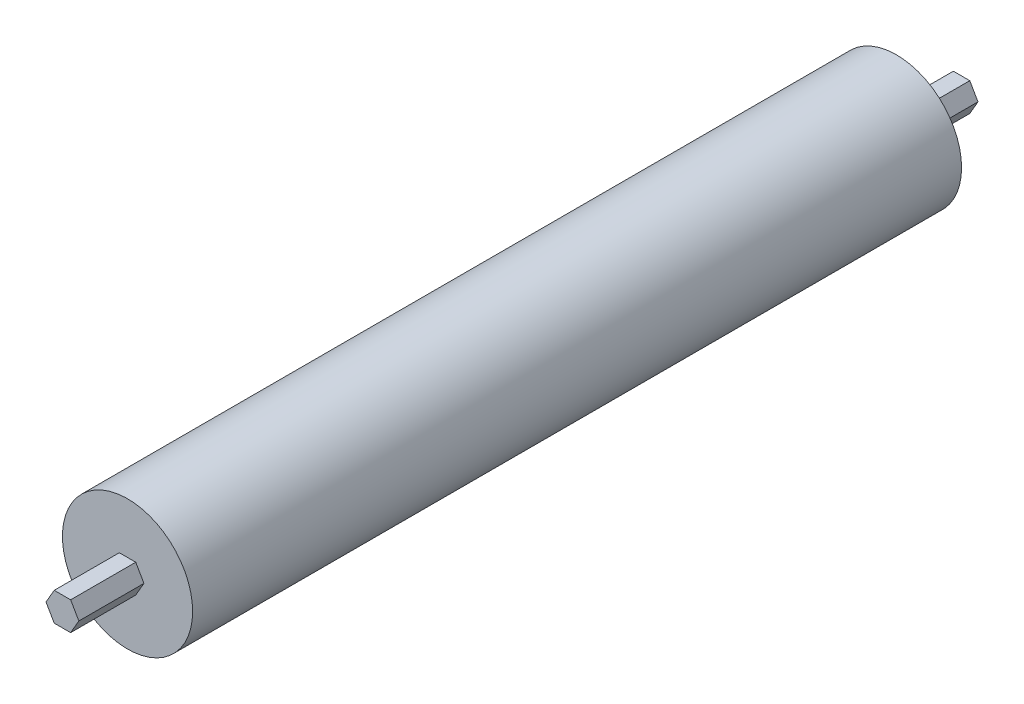
SolidWorks part; units mm, degrees
material "1060 Alloy"
ref_plane "Front Plane" through (0, 0, 0) normal (0, 0, 1) x (1, 0, 0)
ref_plane "Top Plane" through (0, 0, 0) normal (0, 1, 0) x (1, 0, 0)
ref_plane "Right Plane" through (0, 0, 0) normal (1, 0, 0) x (0, 0, -1)
sketch "Sketch1" plane through (0, 0, 0) normal (0, 0, 1) x (1, 0, 0)
  circle A0 centre (0, 0) radius 25.4
  dimension "D1" = 50.8
extrude "Boss-Extrude1" add sketch "Sketch1" along normal blind 300
sketch "Sketch2" plane through (0, 0, 300) normal (0, 0, 1) x (1, 0, 0)
  line L1 (6.4086, 0) -> (3.2043, 5.55)
  line L2 (3.2043, 5.55) -> (-3.2043, 5.55)
  line L3 (-3.2043, 5.55) -> (-6.4086, 0)
  line L4 (-6.4086, 0) -> (-3.2043, -5.55)
  line L5 (-3.2043, -5.55) -> (3.2043, -5.55)
  line L6 (3.2043, -5.55) -> (6.4086, 0)
  circle A0 centre (0, 0) radius 5.55 construction
  dimension "D1" = 11.1
extrude "Boss-Extrude2" add sketch "Sketch2" along normal blind 25.4
sketch "Sketch3" plane through (0, 0, 0) normal (0, 0, -1) x (-1, 0, 0)
  line L1 (6.4086, 0) -> (3.2043, 5.55)
  line L2 (3.2043, 5.55) -> (-3.2043, 5.55)
  line L3 (-3.2043, 5.55) -> (-6.4086, 0)
  line L4 (-6.4086, 0) -> (-3.2043, -5.55)
  line L5 (-3.2043, -5.55) -> (3.2043, -5.55)
  line L6 (3.2043, -5.55) -> (6.4086, 0)
  circle A0 centre (0, 0) radius 5.55 construction
  dimension "D1" = 11.1
extrude "Boss-Extrude3" add sketch "Sketch3" along normal blind 25.4
